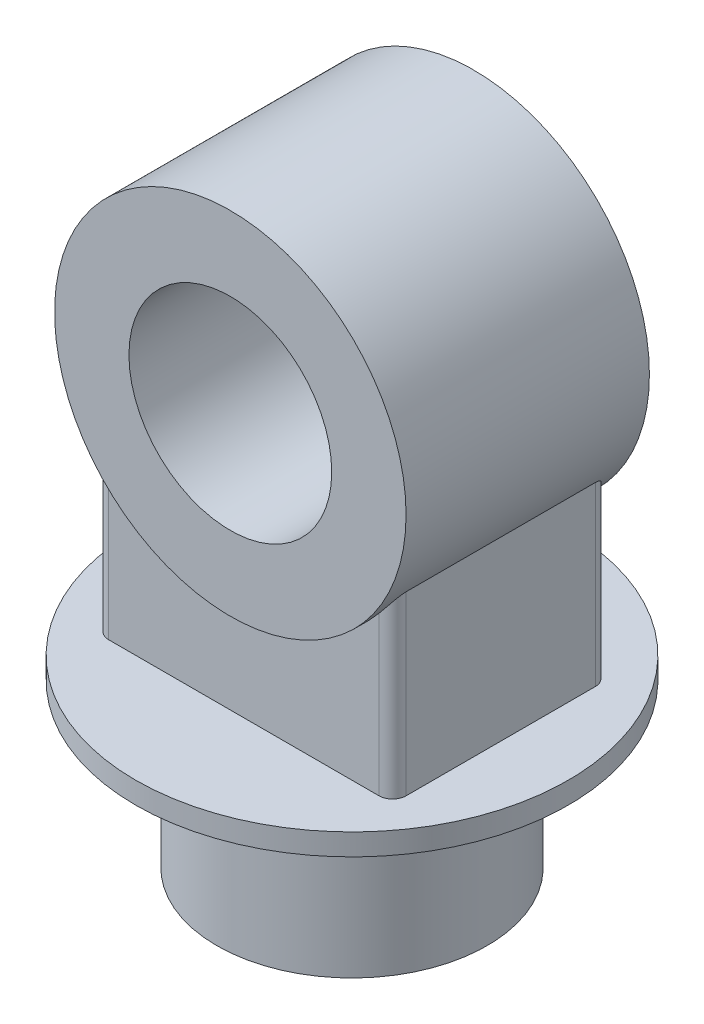
SolidWorks part; units mm, degrees
ref_plane "Front Plane" through (0, 0, 0) normal (0, 0, 1) x (1, 0, 0)
ref_plane "Top Plane" through (0, 0, 0) normal (0, 1, 0) x (1, 0, 0)
ref_plane "Right Plane" through (0, 0, 0) normal (1, 0, 0) x (0, 0, -1)
sketch "Sketch1" plane through (0, 0, 0) normal (0, 1, 0) x (1, 0, 0)
  circle A0 centre (0, 0) radius 100
  dimension "D1" = 200
extrude "Boss-Extrude1" add sketch "Sketch1" along normal blind 120
sketch "Sketch2" plane through (0, 120, 0) normal (0, 1, 0) x (1, 0, 0)
  circle A0 centre (0, 0) radius 160
  dimension "D1" = 320
extrude "Boss-Extrude2" add sketch "Sketch2" along normal blind 16
sketch "Sketch3" plane through (0, 0, 0) normal (0, 0, 1) x (1, 0, 0)
  line L0 (160, 136) -> (-160, 136) construction
  circle A0 centre (0, 336) radius 75
  circle A1 centre (0, 336) radius 130
  dimension "D1" = 150
  dimension "D2" = 260
  dimension "D3" = 200
extrude "Boss-Extrude3" add sketch "Sketch3" along normal mid plane 180 separate body
sketch "Sketch4" plane through (0, 136, 0) normal (0, 1, 0) x (1, 0, 0)
  line L1 (-110, 80) -> (110, 80)
  line L2 (-110, 80) -> (-110, -80)
  line L3 (-110, -80) -> (110, -80)
  line L4 (110, 80) -> (110, -80)
  line L5 (-110, 80) -> (110, -80) construction
  line L6 (-110, -80) -> (110, 80) construction
  point P0 (0, 0)
  dimension "D1" = 160
  dimension "D2" = 220
extrude "Boss-Extrude4" add sketch "Sketch4" along normal up to next
fillet "Fillet1" radius 10 4 edges at (110, 201.359, 80) (110, 201.359, -80) (-110, 201.359, -80) (-110, 201.359, 80)
